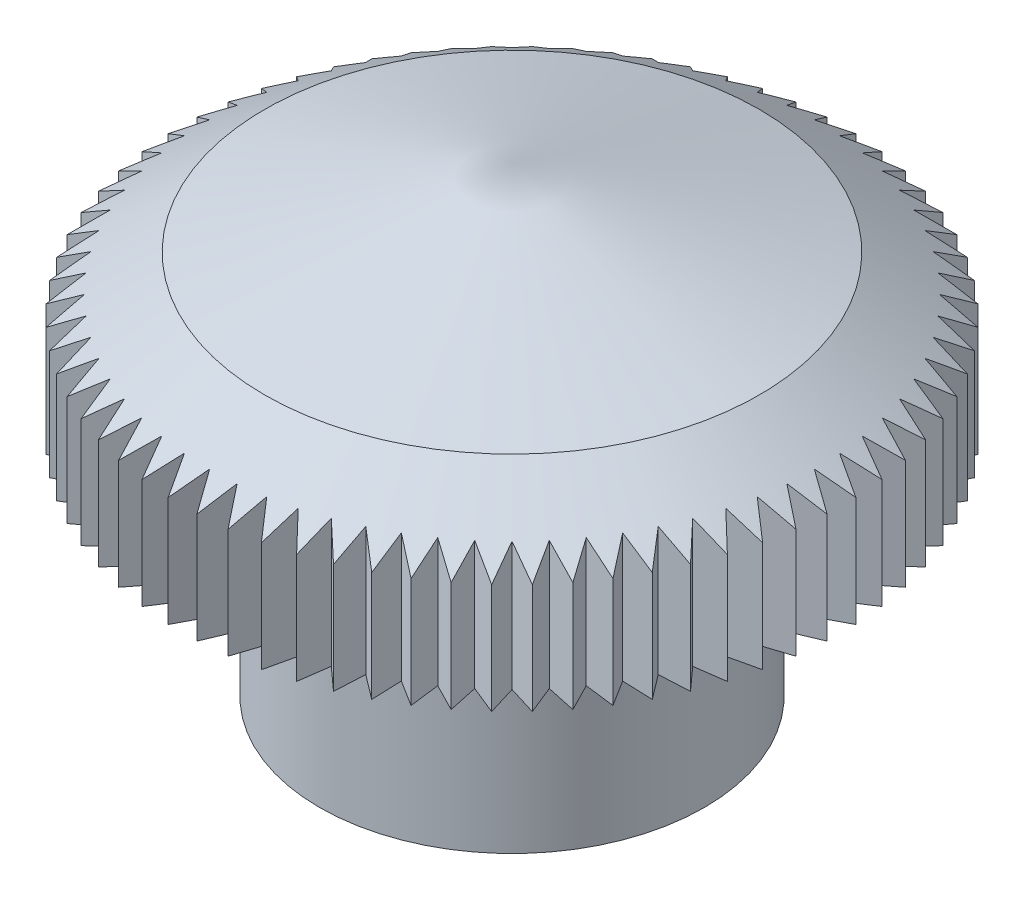
SolidWorks part; units mm, degrees
ref_plane "Alzado" through (0, 0, 0) normal (0, 0, 1) x (1, 0, 0)
ref_plane "Planta" through (0, 0, 0) normal (0, 1, 0) x (1, 0, 0)
ref_plane "Vista lateral" through (0, 0, 0) normal (1, 0, 0) x (0, 0, -1)
sketch "Croquis1" plane through (0, 0, 0) normal (0, 0, 1) x (1, 0, 0)
  line L0 (0, 4.2) -> (0, 0)
  line L1 (0, 4.2) -> (2.25, 3.5)
  line L2 (2.25, 3.5) -> (3, 3)
  line L3 (3, 3) -> (3, 2)
  line L4 (3, 2) -> (1.75, 2)
  line L5 (1.75, 2) -> (1.75, 0)
  line L6 (1.75, 0) -> (1.5, 0)
  line L7 (1.5, 0) -> (1.5, 2)
  line L8 (1.5, 2) -> (1, 2)
  line L9 (1, 2) -> (1, 0)
  line L10 (1, 0) -> (0, 0)
  dimension "D2" = 2
  dimension "D3" = 1.5
  dimension "D4" = 0.25
  dimension "D5" = 1.5
  dimension "D6" = 2.2
  dimension "D7" = 1.25
  dimension "D9" = 2.25
  dimension "D10" = 1
  dimension "D12" = 1
revolve "Revolución1" add sketch "Croquis1" angle 360 about L0
sketch "Croquis3" plane through (0, 0, 0) normal (0, 1, 0) x (1, 0, 0)
  line L0 (0, 0) -> (-0.1309, 2.9971) construction
  line L1 (0, 0) -> (0.1309, 2.9971) construction
  line L2 (-0.1309, 2.9971) -> (0, 2.75)
  line L3 (0, 0) -> (0, 3) construction
  line L4 (0, 2.75) -> (0.1309, 2.9971)
  circle A0 centre (0, 0) radius 3 construction
  arc A1 (0.1309, 2.9971) -> (-0.1309, 2.9971) centre (0, 0) ccw
  circle A2 centre (0, 0) radius 2.75 construction
  dimension "D2" = 5.5
  dimension "D1" = 2.5
  dimension "D3" = 2.5
extrude "Cortar-Extruir1" cut sketch "Croquis3" along normal through all
pattern_circular "MatrizC1" count 72 over 360 about axis through (0, 0, 0) along (0, 1, 0) of "Cortar-Extruir1"
hole_wizard "Taladro roscado M1x0.251" positions "Croquis5" profile "Croquis4" tap size "M1x0.25" standard "KS"
sketch "Croquis5" plane through (0, 0, 0) normal (0, -1, 0) x (1, 0, 0)
  circle A0 centre (0, 0) radius 1 construction
  point P0 (0, 0)
cosmetic thread "Rosca de taladro1" parameters "D1"=2, "D2"=1
sketch "Croquis4" plane through (0, 0, 0) normal (1, 0, 0) x (0, 0, -1)
  line L0 (0, 0) -> (0, 2.7253)
  line L1 (0, 2.7253) -> (0.375, 2.5)
  line L2 (0.375, 2.5) -> (0.375, 0)
  line L5 (0.375, 0) -> (0, 0)
  line L10 (0, 2.7253) -> (-0.375, 2.5) construction
  line L11 (0, -6.35) -> (0, 107.95) construction
  dimension "Diámetro de perforador para roscar" = 0.75
  dimension "Profundidad de perforador para roscar" = 2.5
  dimension "Ángulo de perforador" = 118
